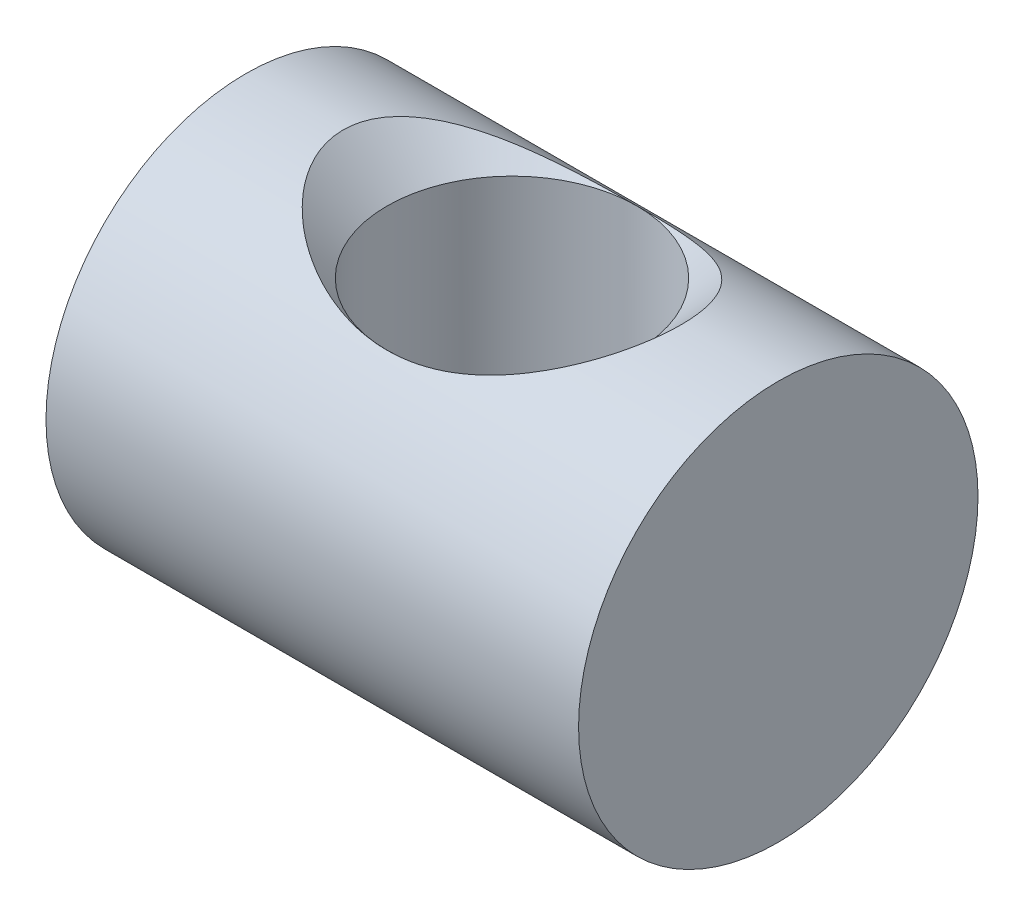
SolidWorks part; units mm, degrees
ref_plane "Płaszczyzna przednia" through (0, 0, 0) normal (0, 0, 1) x (1, 0, 0)
ref_plane "Płaszczyzna górna" through (0, 0, 0) normal (0, 1, 0) x (1, 0, 0)
ref_plane "Płaszczyzna prawa" through (0, 0, 0) normal (1, 0, 0) x (0, 0, -1)
sketch "Szkic1" plane through (0, 0, 0) normal (1, 0, 0) x (0, 0, -1)
  circle A0 centre (0, 0) radius 15
extrude "Dodanie-wyciągnięcie1" add sketch "Szkic1" along normal mid plane 40
ref_plane "Płaszczyzna1" [suppressed] through (0, 15, 0) normal (0, 1, 0) x (1, 0, 0)
sketch "Sketch1" plane through (0, 0, 0) normal (0, 1, 0) x (1, 0, 0)
  circle A0 centre (0, 0) radius 9.3853
extrude "Cut-Extrude1" cut sketch "Sketch1" against normal blind 23 and the other way blind 34
sketch "Sketch2" plane through (0, 0, 0) normal (1, 0, 0) x (0, 0, -1)
  line L0 (0, 2.3158) -> (0, 32.7567)
  line L1 (0, 32.7567) -> (-30.4409, 32.7567)
  line L2 (-30.4409, 32.7567) -> (0, 2.3158)
  point P4 (-9.3853, 11.7011)
  dimension "D1" = 45
revolve "Cut-Revolve1" cut sketch "Sketch2" angle 360 about L0
